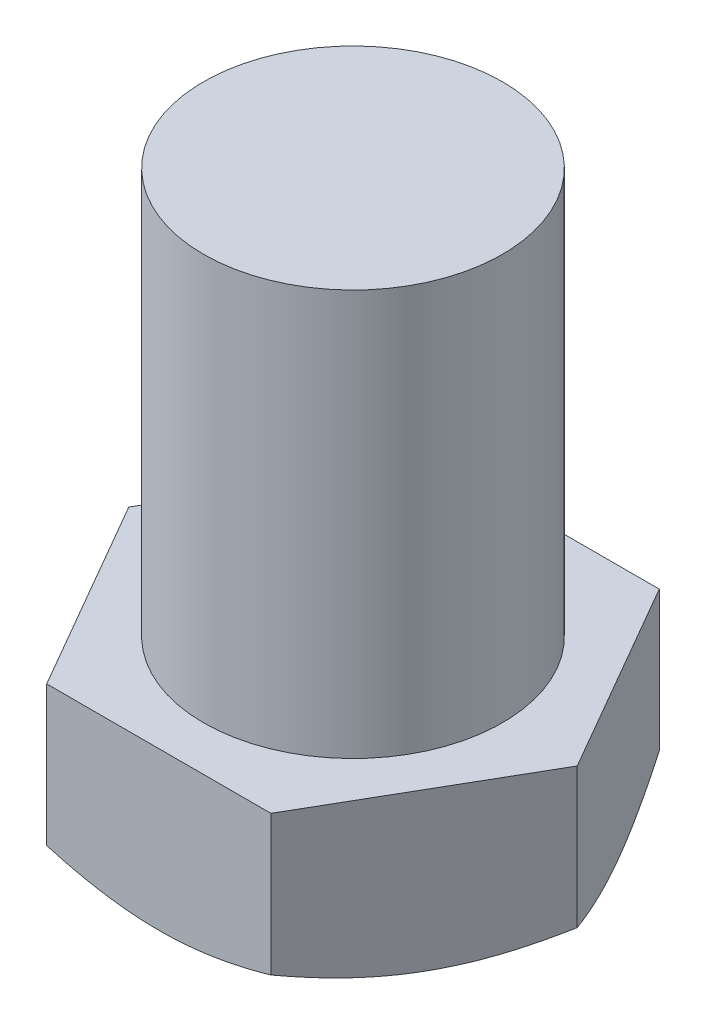
SolidWorks part; units mm, degrees
ref_plane "Спереди" through (0, 0, 0) normal (0, 0, 1) x (1, 0, 0)
ref_plane "Сверху" through (0, 0, 0) normal (0, 1, 0) x (1, 0, 0)
ref_plane "Справа" through (0, 0, 0) normal (1, 0, 0) x (0, 0, -1)
other "Configuration Table"
sketch "Эскиз1" plane through (0, 0, 0) normal (0, 1, 0) x (1, 0, 0)
  line L1 (10.5, 0) -> (5.25, 9.0933)
  line L2 (5.25, 9.0933) -> (-5.25, 9.0933)
  line L3 (-5.25, 9.0933) -> (-10.5, 0)
  line L4 (-10.5, 0) -> (-5.25, -9.0933)
  line L5 (-5.25, -9.0933) -> (5.25, -9.0933)
  line L6 (5.25, -9.0933) -> (10.5, 0)
  circle A0 centre (0, 0) radius 10.5 construction
  dimension "D1" = 21
extrude "Бобышка-Вытянуть1" add sketch "Эскиз1" along normal blind 8
sketch "Эскиз2" plane through (0, 8, 0) normal (0, 1, 0) x (1, 0, 0)
  circle A0 centre (0, 0) radius 7
  dimension "D1" = 14
extrude "Бобышка-Вытянуть2" add sketch "Эскиз2" along normal blind 19
sketch "Эскиз3" plane through (0, 0, 0) normal (0, -1, 0) x (1, 0, 0)
  circle A0 centre (0, 0) radius 8
  dimension "D1" = 16
extrude "Вырез-Вытянуть2" cut sketch "Эскиз3" against normal blind 1.5 draft 60 flip side to cut contours A0
